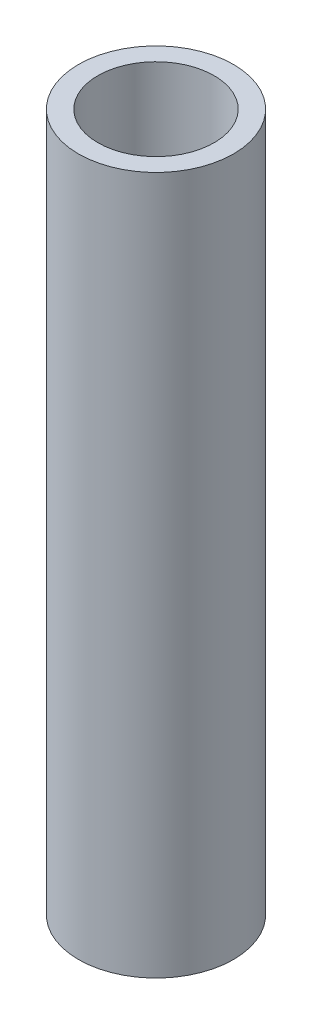
SolidWorks part; units mm, degrees
ref_plane "Front Plane" through (0, 0, 0) normal (0, 0, 1) x (1, 0, 0)
ref_plane "Top Plane" through (0, 0, 0) normal (0, 1, 0) x (1, 0, 0)
ref_plane "Right Plane" through (0, 0, 0) normal (1, 0, 0) x (0, 0, -1)
sketch "Sketch1" plane through (0, 0, 0) normal (0, 1, 0) x (1, 0, 0)
  circle A0 centre (0, 0) radius 12.7
  circle A1 centre (0, 0) radius 9.525
  dimension "D1" = 19.05
  dimension "D2" = 25.4
extrude "Boss-Extrude2" add sketch "Sketch1" along normal blind 114.3
